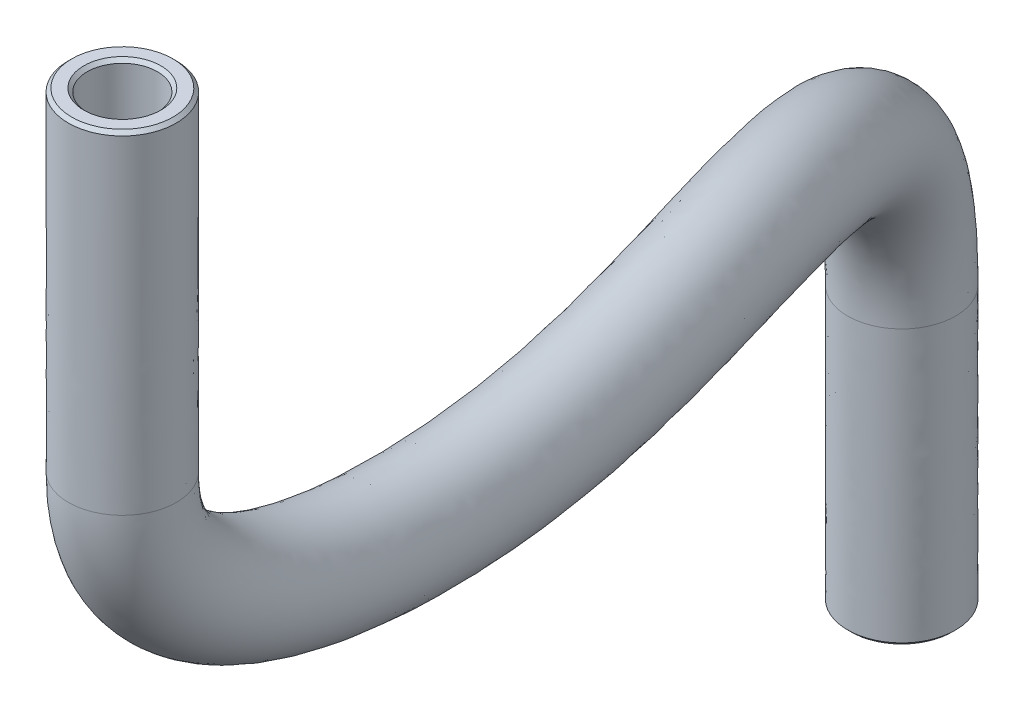
SolidWorks part; units mm, degrees
ref_plane "Front Plane" through (0, 0, 0) normal (0, 0, 1) x (1, 0, 0)
ref_plane "Top Plane" through (0, 0, 0) normal (0, 1, 0) x (1, 0, 0)
ref_plane "Right Plane" through (0, 0, 0) normal (1, 0, 0) x (0, 0, -1)
sketch3d "3DSketch1"
  line L0 (104.325, -62.025, 13.85) -> (104.325, -74.325, 13.85)
  line L1 (93.825, -93.2823, -25.525) -> (93.825, -103.4823, -25.525)
  spline S0 degree 3 poles (104.325, -74.325, 13.85) (104.325, -80.9108, 13.85) (104.7765, -83.5091, -5.8375) (93.825, -83.3301, -25.525) (93.825, -93.2823, -25.525) knots 0 0 0 0 0.439595 1 1 1 1
sketch "Sketch1" plane through (0, -95.3823, 0) normal (0, 1, 0) x (1, 0, 0)
  circle A0 centre (93.825, 25.525) radius 1.3
  circle A1 centre (93.825, 25.525) radius 2
  circle A2 centre (93.825, 25.525) radius 3.6 construction
  dimension "D1" = 4
  dimension "D2" = 2.6
sweep "Sweep1" add profiles "Sketch1" path "3DSketch1"
chamfer "Chamfer1" distance 0.127 angle 45 4 edges at (91.825, -103.4823, -25.525) (92.525, -103.4823, -25.525) (103.5967, -62.025, 11.9873) (103.8516, -62.025, 12.6393)
